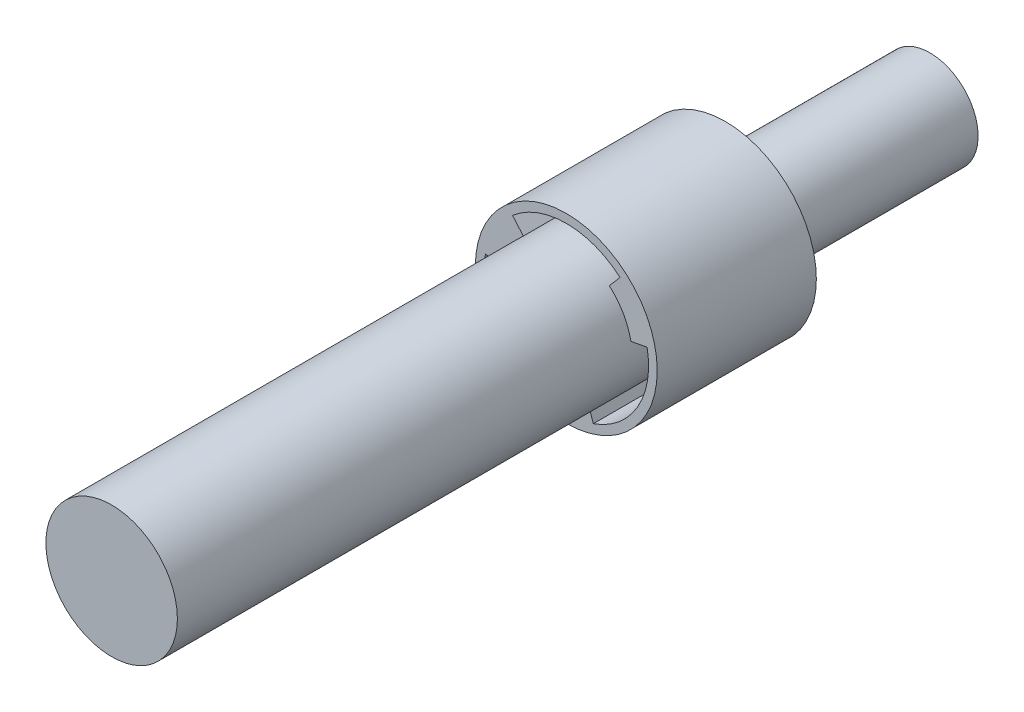
SolidWorks part; units mm, degrees
ref_plane "Front Plane" through (0, 0, 0) normal (0, 0, 1) x (1, 0, 0)
ref_plane "Top Plane" through (0, 0, 0) normal (0, 1, 0) x (1, 0, 0)
ref_plane "Right Plane" through (0, 0, 0) normal (1, 0, 0) x (0, 0, -1)
sketch "Sketch1" plane through (0, 0, 0) normal (0, 0, 1) x (1, 0, 0)
  circle A0 centre (0, 0) radius 14.6939
  dimension "D1" = 29.3878
extrude "Boss-Extrude1" add sketch "Sketch1" along normal blind 101.6
sketch "Sketch2" plane through (0, 0, 0) normal (0, 0, -1) x (-1, 0, 0)
  circle A0 centre (0, 0) radius 20.32
  dimension "D1" = 40.64
extrude "Boss-Extrude2" add sketch "Sketch2" along normal blind 35.56
sketch "Sketch3" plane through (0, 0, -35.56) normal (0, 0, -1) x (-1, 0, 0)
  circle A0 centre (0, 0) radius 10.7442
  dimension "D1" = 21.4884
extrude "Boss-Extrude3" add sketch "Sketch3" along normal blind 45.72
sketch "Sketch4" plane through (0, 0, 0) normal (0, 0, 1) x (1, 0, 0)
  line L0 (0, 0) -> (0, 20.32) construction
  circle A0 centre (0, 0) radius 20.32 construction
sketch "Sketch5" plane through (0, 0, 0) normal (0, 0, 1) x (1, 0, 0)
  line L0 (0, 0) -> (0, 20.32) construction
  line L1 (0, 0) -> (0, 20.32)
  line L2 (0, 0) -> (0, -18.3896) construction
  line L3 (0, 0) -> (6.0452, -17.3676)
  line L4 (0, 0) -> (-6.0452, -17.3676)
  line L5 (-6.0452, -17.3676) -> (6.0452, -17.3676) construction
  line L6 (0, 0) -> (-15.9259, 9.1948) construction
  line L7 (-12.0182, 13.9191) -> (-18.0634, 3.4485) construction
  line L8 (0, 0) -> (-18.0634, 3.4485)
  line L9 (0, 0) -> (-12.0182, 13.9191)
  line L10 (0, 0) -> (15.9259, 9.1948) construction
  line L11 (18.0634, 3.4485) -> (12.0182, 13.9191) construction
  line L12 (0, 0) -> (12.0182, 13.9191)
  line L13 (0, 0) -> (18.0634, 3.4485)
  circle A0 centre (0, 0) radius 20.32 construction
  circle A1 centre (0, 0) radius 20.32
  circle A2 centre (0, 0) radius 18.3896
  circle A3 centre (0, 0) radius 14.6939 construction
  circle A4 centre (0, 0) radius 14.6939
  point P22 (0, 0)
  circle M3 centre (0, 0) radius 14.6939
  dimension "D2" = 12.0904
  dimension "D1" = 1.9304
  dimension "D3" = 3
extrude "Cut-Extrude1" cut sketch "Sketch5" against normal blind 14.1986 contours A2 M3 | L3 A2 L13 M3 | L12 A2 L1 M3 | L1 A2 L9 M3
